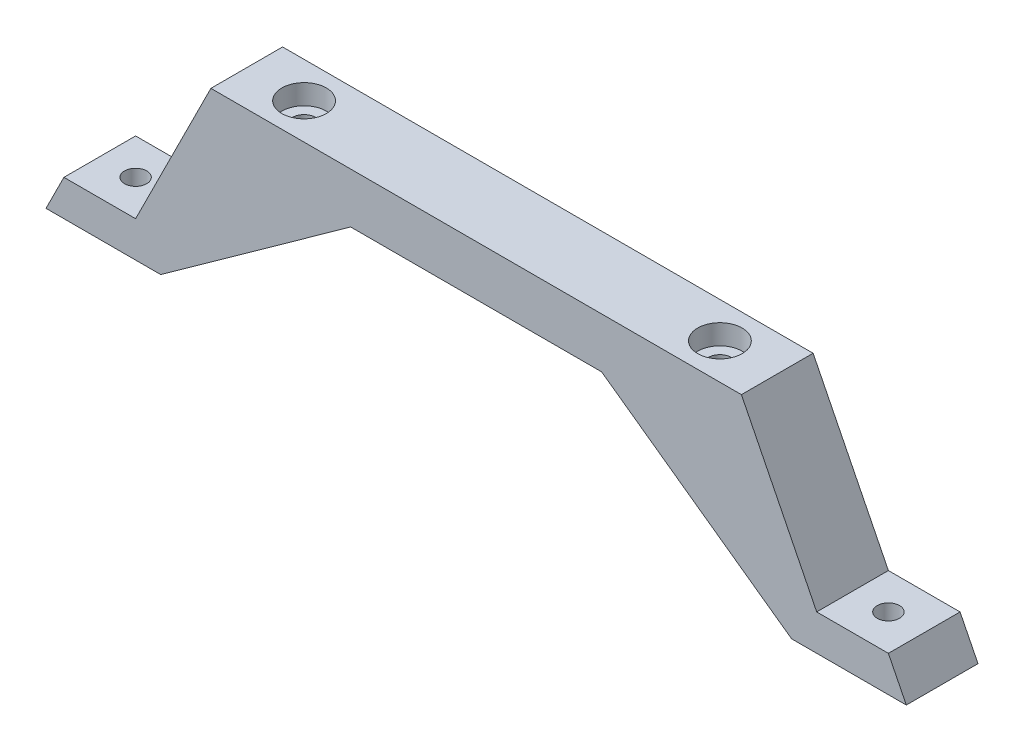
SolidWorks part; units mm, degrees
ref_plane "前视基准面" through (0, 0, 0) normal (0, 0, 1) x (1, 0, 0)
ref_plane "上视基准面" through (0, 0, 0) normal (0, 1, 0) x (1, 0, 0)
ref_plane "右视基准面" through (0, 0, 0) normal (1, 0, 0) x (0, 0, -1)
sketch "草图1" plane through (0, 0, 0) normal (0, 0, 1) x (1, 0, 0)
  line L0 (33.8113, 38.6957) -> (33.8113, -40.812) construction
  line L1 (-3.1887, 13.0528) -> (33.8113, 13.0528)
  line L2 (-13.6887, -7.9472) -> (-23.6887, -7.9472)
  line L3 (-26.1887, -12.9472) -> (-10.1887, -12.9472)
  line L4 (33.8113, 13.0528) -> (33.8113, 6.0528)
  line L5 (16.3113, 6.0528) -> (33.8113, 6.0528)
  line L8 (-13.6887, -7.9472) -> (-3.1887, 13.0528)
  line L9 (-23.6887, -7.9472) -> (-26.1887, -12.9472)
  line L11 (-10.1887, -12.9472) -> (16.3113, 6.0528)
  point P0 (33.8113, 9.5528)
  point P10 (-16.1887, -12.9472)
extrude "凸台-拉伸1" add sketch "草图1" along normal blind 10
mirror "镜向1" about plane through (33.8113, 13.0528, 10) normal (-1, 0, 0) of "凸台-拉伸1"
sketch "草图2" plane through (0, 13.0528, 0) normal (0, 1, 0) x (1, 0, 0)
  line L0 (70.8113, 0) -> (-3.1887, 0) construction
  line L1 (33.8113, 13.863) -> (33.8113, -35.9161) construction
  line L2 (-3.1887, -5) -> (77.4405, -5) construction
  line L3 (-3.1887, -10) -> (-3.1887, 0) construction
  circle A2 centre (4.8113, -5) radius 1.6
  circle A3 centre (62.8113, -5) radius 1.6
  point P0 (33.8113, 0)
  dimension "D1" = 3.2
  dimension "D4" = 3.2
  dimension "D5" = 29
  dimension "D6" = 29
extrude "切除-拉伸2" cut sketch "草图2" against normal through all
sketch "草图3" plane through (0, 13.0528, 0) normal (0, 1, 0) x (1, 0, 0)
  circle A0 centre (4.8113, -5) radius 3.1
  circle A1 centre (62.8113, -5) radius 3.1
  dimension "D1" = 6.2
  dimension "D2" = 6.2
extrude "切除-拉伸3" cut sketch "草图3" against normal blind 2.8
sketch "草图5" plane through (0, -7.9472, 0) normal (0, 1, 0) x (1, 0, 0)
  line L0 (4.8113, -5) -> (-28.7911, -5) construction
  line L1 (-23.6887, -10) -> (-23.6887, 0) construction
  line L2 (62.8113, -5) -> (99.3823, -5) construction
  line L3 (91.3113, -10) -> (91.3113, 0) construction
  circle A0 centre (-18.6887, -5) radius 1.55
  circle A1 centre (86.3113, -5) radius 1.55
  dimension "D2" = 3.1
  dimension "D4" = 3.1
  dimension "D1" = 5
  dimension "D3" = 5
extrude "切除-拉伸4" cut sketch "草图5" against normal through all
